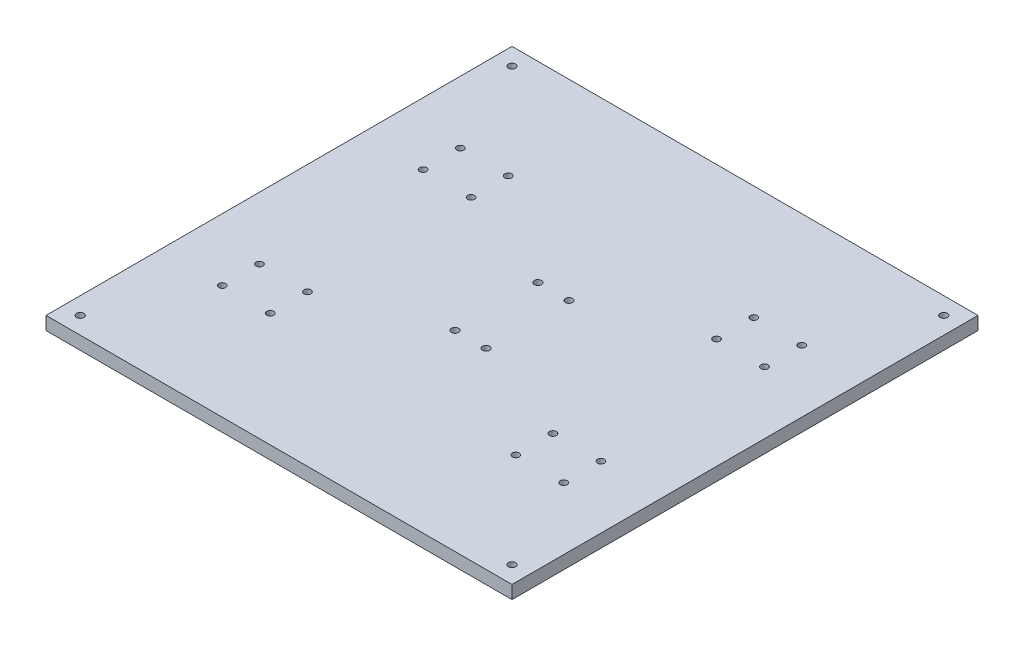
SolidWorks part; units mm, degrees
ref_plane "Front Plane" through (0, 0, 0) normal (0, 0, 1) x (1, 0, 0)
ref_plane "Top Plane" through (0, 0, 0) normal (0, 1, 0) x (1, 0, 0)
ref_plane "Right Plane" through (0, 0, 0) normal (1, 0, 0) x (0, 0, -1)
sketch "Sketch1" plane through (0, 0, 0) normal (0, 1, 0) x (1, 0, 0)
  line L1 (0, 0) -> (225, 0)
  line L2 (0, 0) -> (0, 225)
  line L3 (0, 225) -> (225, 225)
  line L4 (225, 0) -> (225, 225)
  line L5 (0, 0) -> (225, 225) construction
  line L6 (0, 225) -> (225, 0) construction
  point P4 (112.5, 112.5)
  dimension "D1" = 225
  dimension "D2" = 225
extrude "Boss-Extrude1" add sketch "Sketch1" along normal blind 6.35
sketch "Sketch2" plane through (0, 6.35, 0) normal (0, 1, 0) x (1, 0, 0)
  line L0 (222.5, 222.5) -> (222.5, 225) construction
  line L1 (2.5, 2.5) -> (222.5, 2.5) construction
  line L2 (2.5, 2.5) -> (2.5, 222.5) construction
  line L3 (2.5, 222.5) -> (222.5, 222.5) construction
  line L4 (222.5, 2.5) -> (222.5, 222.5) construction
  line L5 (112.5, 222.5) -> (112.5, 2.5) construction
  line L6 (2.5, 112.5) -> (222.5, 112.5) construction
  line L7 (225, 225) -> (0, 225) construction
  line L8 (222.5, 222.5) -> (225, 222.5) construction
  line L9 (225, 0) -> (225, 225) construction
  line L10 (2.5, 2.5) -> (0, 2.5) construction
  line L11 (0, 225) -> (0, 0) construction
  line L12 (2.5, 2.5) -> (2.5, 0) construction
  line L13 (0, 0) -> (225, 0) construction
  circle A0 centre (216.74, 216.74) radius 1.75
  circle A1 centre (8.26, 216.74) radius 1.75
  circle A2 centre (216.74, 8.26) radius 1.75
  circle A3 centre (8.26, 8.26) radius 1.75
  dimension "D2" = 5.76
  dimension "D4" = 3.5
  dimension "D1" = 220
  dimension "D3" = 5.76
extrude "Cut-Extrude1" cut sketch "Sketch2" against normal through all
sketch "Sketch3" plane through (0, 6.35, 0) normal (0, 1, 0) x (1, 0, 0)
  line L0 (112.5, 0) -> (112.5, 225) construction
  line L1 (105, 92.5) -> (120, 92.5) construction
  line L2 (105, 92.5) -> (105, 132.5) construction
  line L3 (105, 132.5) -> (120, 132.5) construction
  line L4 (120, 92.5) -> (120, 132.5) construction
  line L5 (105, 92.5) -> (120, 132.5) construction
  line L6 (105, 132.5) -> (120, 92.5) construction
  line L7 (0, 0) -> (225, 0) construction
  line L8 (225, 225) -> (0, 225) construction
  line L9 (0, 112.5) -> (225, 112.5) construction
  line L10 (0, 225) -> (0, 0) construction
  line L11 (225, 0) -> (225, 225) construction
  circle A0 centre (120, 132.5) radius 1.75
  circle A1 centre (120, 92.5) radius 1.75
  circle A2 centre (105, 92.5) radius 1.75
  circle A3 centre (105, 132.5) radius 1.75
  point P4 (112.5, 112.5)
  dimension "D3" = 3.5
  dimension "D1" = 15
  dimension "D2" = 40
extrude "Cut-Extrude2" cut sketch "Sketch3" against normal through all
sketch "Sketch4" plane through (0, 0, 0) normal (0, -1, 0) x (1, 0, 0)
  line L0 (225, 0) -> (225, -225) construction
  line L1 (171.76, -55.04) -> (194.92, -55.04) construction
  line L2 (171.76, -55.04) -> (171.76, -72.99) construction
  line L3 (171.76, -72.99) -> (194.92, -72.99) construction
  line L4 (194.92, -55.04) -> (194.92, -72.99) construction
  line L5 (112.5, 0) -> (112.5, -225) construction
  line L6 (225, -225) -> (0, -225) construction
  line L7 (0, 0) -> (225, 0) construction
  line L8 (0, -112.5) -> (225, -112.5) construction
  line L9 (0, -225) -> (0, 0) construction
  line L10 (194.92, -169.96) -> (194.92, -152.01) construction
  line L11 (171.76, -152.01) -> (194.92, -152.01) construction
  line L12 (171.76, -169.96) -> (171.76, -152.01) construction
  line L13 (171.76, -169.96) -> (194.92, -169.96) construction
  circle A0 centre (171.76, -55.04) radius 1.675
  circle A1 centre (194.92, -55.04) radius 1.675
  circle A2 centre (194.92, -72.99) radius 1.675
  circle A3 centre (171.76, -72.99) radius 1.675
  circle A4 centre (30.08, -72.99) radius 1.675
  circle A5 centre (53.24, -72.99) radius 1.675
  circle A6 centre (53.24, -55.04) radius 1.675
  circle A7 centre (30.08, -55.04) radius 1.675
  circle A8 centre (30.08, -169.96) radius 1.675
  circle A9 centre (53.24, -169.96) radius 1.675
  circle A10 centre (53.24, -152.01) radius 1.675
  circle A11 centre (30.08, -152.01) radius 1.675
  circle A12 centre (171.76, -152.01) radius 1.675
  circle A13 centre (194.92, -152.01) radius 1.675
  circle A14 centre (194.92, -169.96) radius 1.675
  circle A15 centre (171.76, -169.96) radius 1.675
  dimension "D5" = 3.35
  dimension "D1" = 23.16
  dimension "D2" = 17.95
  dimension "D3" = 30.08
  dimension "D4" = 55.04
extrude "Cut-Extrude3" cut sketch "Sketch4" against normal through all
